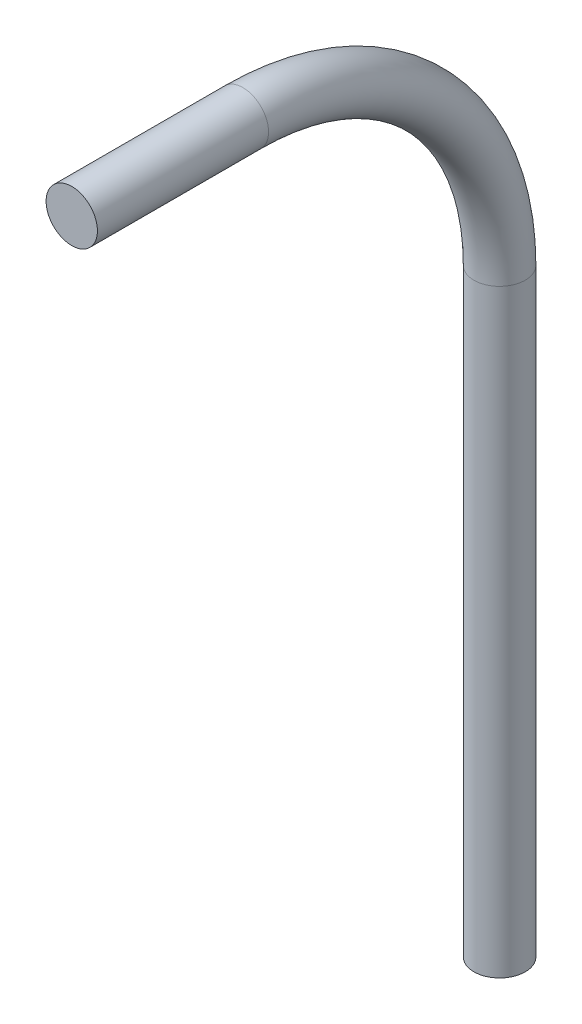
SolidWorks part; units mm, degrees
ref_plane "Plane1" through (0, 0, 0) normal (0, 0, 1) x (1, 0, 0)
ref_plane "Plane2" through (0, 0, 0) normal (0, 1, 0) x (1, 0, 0)
ref_plane "Plane3" through (0, 0, 0) normal (1, 0, 0) x (0, 0, -1)
sketch "Sketch1" plane through (0, 0, 0) normal (0, 0, 1) x (1, 0, 0)
  circle A0 centre (0, 0) radius 3
  dimension "D1" = 6
sketch "Sketch3" plane through (0, 0, 0) normal (1, 0, 0) x (0, 0, -1)
  line L0 (0, 0) -> (20, 0)
  line L1 (50, -30) -> (50, -100)
  arc A0 (20, 0) -> (50, -30) centre (20, -30) cw
  dimension "D1" = 30
  dimension "D2" = 20
  dimension "D3" = 90
  dimension "D4" = 70
sweep "Sweep1" add profiles "Sketch1" path "Sketch3"
